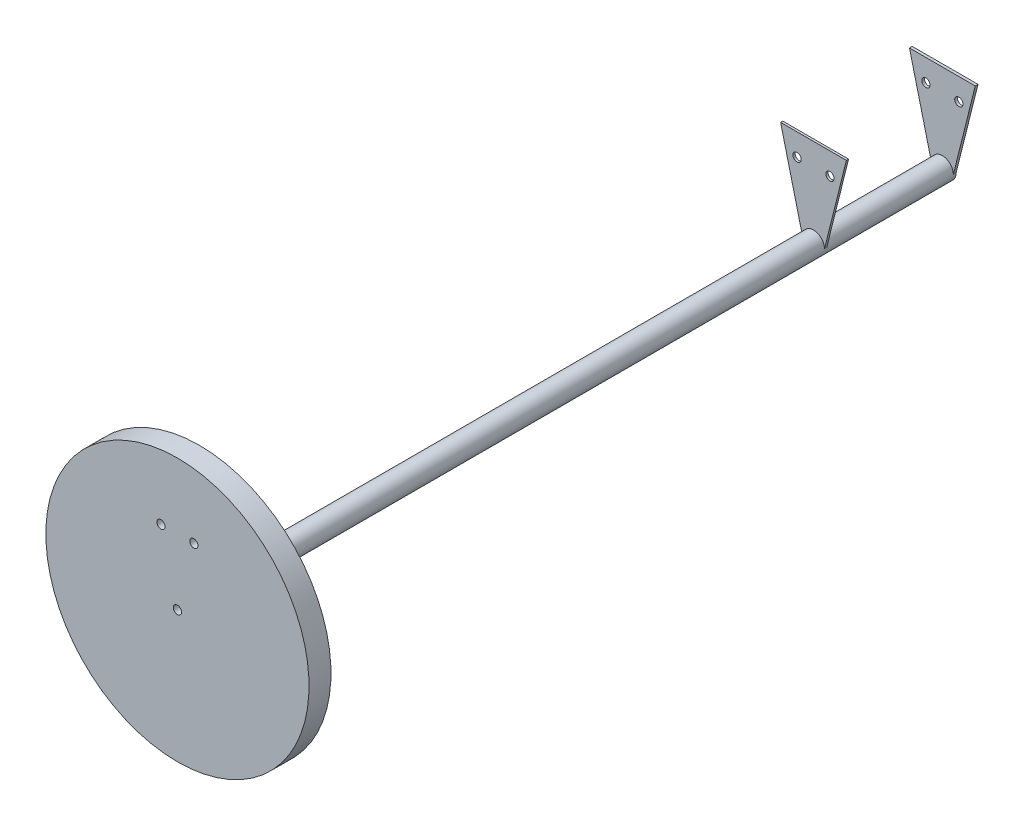
SolidWorks part; units mm, degrees
ref_plane "Front Plane" through (0, 0, 0) normal (0, 0, 1) x (1, 0, 0)
ref_plane "Top Plane" through (0, 0, 0) normal (0, 1, 0) x (1, 0, 0)
ref_plane "Right Plane" through (0, 0, 0) normal (1, 0, 0) x (0, 0, -1)
sketch "Sketch1" plane through (0, 0, 0) normal (1, 0, 0) x (0, 0, -1)
  line L0 (-444.5, 0) -> (444.5, 0)
  line L1 (-444.5, 0) -> (-444.5, 152.4)
  line L2 (-444.5, 152.4) -> (-419.1, 152.4)
  line L3 (-419.1, 152.4) -> (-419.1, 12.7)
  line L4 (-419.1, 12.7) -> (444.5, 12.7)
  line L5 (444.5, 12.7) -> (444.5, 0)
  point P0 (88.9, 0)
  point P4 (0, 0)
  dimension "D1" = 152.4
  dimension "D2" = 25.4
  dimension "D3" = 12.7
  dimension "D4" = 889
  dimension "D5" = 355.6
revolve "OAL Revolve" add sketch "Sketch1" angle 360 about L0
sketch "Sketch3" plane through (0, 0, -444.5) normal (0, 0, -1) x (-1, 0, 0)
  line L0 (12.7, 0) -> (-12.7, 0)
  line L1 (-12.7, 0) -> (-38.1, 101.6)
  line L2 (-38.1, 101.6) -> (38.1, 101.6)
  line L3 (0, 0) -> (0, 152.4) construction
  line L4 (0, 101.6) -> (0, 0) construction
  line L5 (12.7, 0) -> (38.1, 101.6)
  dimension "D1" = 101.6
  dimension "D2" = 38.1
  dimension "D3" = 12.7
extrude "End Tab 1" add sketch "Sketch3" against normal blind 3.175
sketch "Sketch4" plane through (0, 0, -444.5) normal (0, 0, -1) x (-1, 0, 0)
  line L0 (0, 101.6) -> (0, 76.2) construction
  line L1 (38.1, 101.6) -> (-38.1, 101.6) construction
  line L2 (0, 0) -> (0, 152.4) construction
  line L3 (0, 76.2) -> (-19.05, 76.2) construction
  line L4 (0, 76.2) -> (0, 0) construction
  circle A0 centre (-19.05, 76.2) radius 4.7625
  circle A1 centre (19.05, 76.2) radius 4.7625
  circle A2 centre (0, 0) radius 4.7625
  dimension "D3" = 9.525
  dimension "D4" = 9.525
  dimension "D1" = 76.2
  dimension "D2" = 19.05
extrude "End Tab 1 Cut" cut sketch "Sketch4" against normal through all
ref_plane "Plane1" through (0, 0, -292.1) normal (0, 0, -1) x (-1, 0, 0)
sketch "Sketch5" plane through (0, 0, -292.1) normal (0, 0, -1) x (-1, 0, 0)
  line L0 (-38.1, 101.6) -> (-12.7, 0) construction
  line L1 (12.7, 0) -> (38.1, 101.6)
  line L2 (38.1, 101.6) -> (-38.1, 101.6)
  line L3 (-38.1, 101.6) -> (-12.7, 0)
  arc A0 (-12.7, 0) -> (12.7, 0) centre (0, 0) cw
  arc A1 (12.7, 0) -> (-12.7, 0) centre (0, 0) ccw construction
  circle A2 centre (19.05, 76.2) radius 4.7625
  circle A3 centre (-19.05, 76.2) radius 4.7625
  dimension "D1" = 9.525
extrude "Boss-Extrude1" add sketch "Sketch5" along normal blind 2.54
